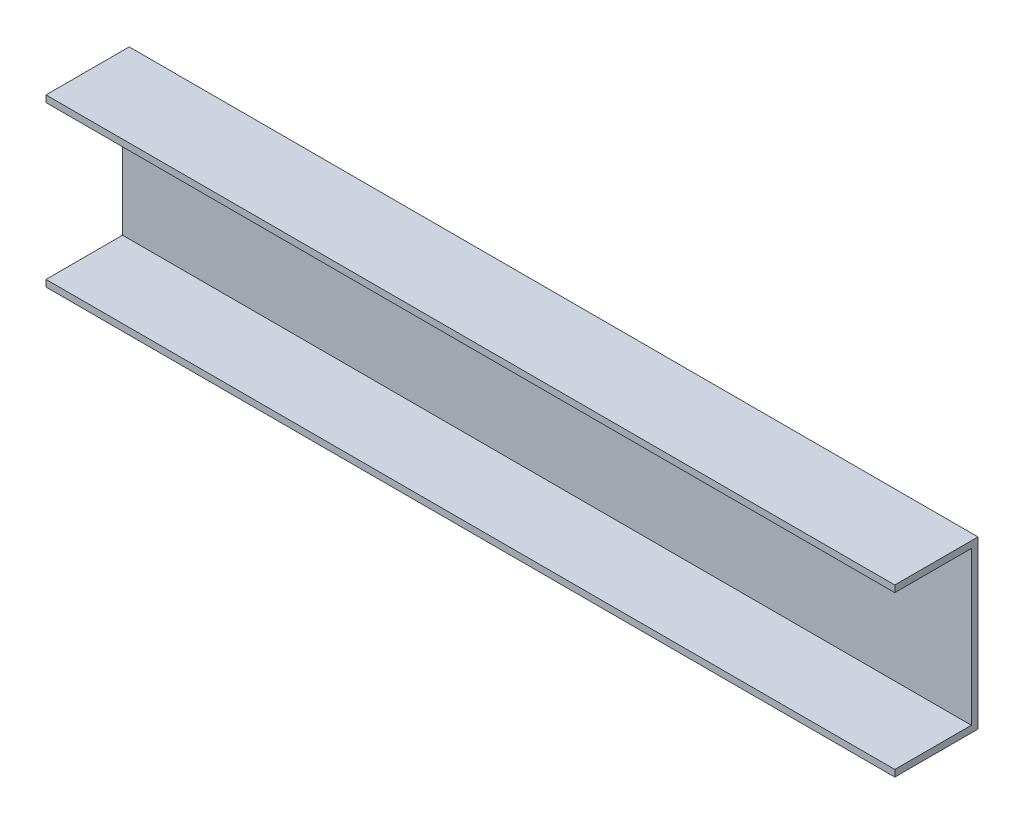
SolidWorks part; units mm, degrees
ref_plane "Front Plane" through (0, 0, 0) normal (0, 0, 1) x (1, 0, 0)
ref_plane "Top Plane" through (0, 0, 0) normal (0, 1, 0) x (1, 0, 0)
ref_plane "Right Plane" through (0, 0, 0) normal (1, 0, 0) x (0, 0, -1)
sketch "Sketch1" plane through (0, 0, 0) normal (1, 0, 0) x (0, 0, -1)
  line L0 (0, 24.378) -> (23, 24.378)
  line L1 (0, 26.378) -> (25, 26.378)
  line L2 (0, 26.378) -> (0, 24.378)
  line L3 (0, -23.622) -> (25, -23.622)
  line L4 (25, 26.378) -> (25, -23.622)
  line L5 (23, 24.378) -> (23, -21.622)
  line L6 (23, -21.622) -> (0, -21.622)
  line L7 (0, -21.622) -> (0, -23.622)
  point P6 (11.5, -21.622)
  dimension "D1" = 50
  dimension "D2" = 2
  dimension "D3" = 2
  dimension "D4" = 2
  dimension "D5" = 25
extrude "Boss-Extrude1" add sketch "Sketch1" along normal blind 175
sketch "Sketch2" plane through (0, 0, -25) normal (0, 0, -1) x (-1, 0, 0)
  line L0 (-175, -23.622) -> (0, -23.622) construction
  line L1 (0, -23.622) -> (0, 26.378) construction
  circle A0 centre (-30, 6.378) radius 2.55
  dimension "D1" = 30
  dimension "D2" = 30
extrude "Cut-Extrude1" cut sketch "Sketch2" against normal blind 380
sketch "Sketch3" plane through (0, 0, 0) normal (-1, 0, 0) x (0, 0, 1)
  line L0 (0, 26.378) -> (-25, 26.378)
  line L1 (-25, 26.378) -> (-25, -23.622)
  line L2 (-25, -23.622) -> (0, -23.622)
  line L3 (0, -23.622) -> (0, -21.622)
  line L4 (0, -21.622) -> (-23, -21.622)
  line L5 (-23, -21.622) -> (-23, 24.378)
  line L6 (-23, 24.378) -> (0, 24.378)
  line L7 (0, 24.378) -> (0, 26.378)
extrude "Boss-Extrude2" add sketch "Sketch3" along normal blind 80
